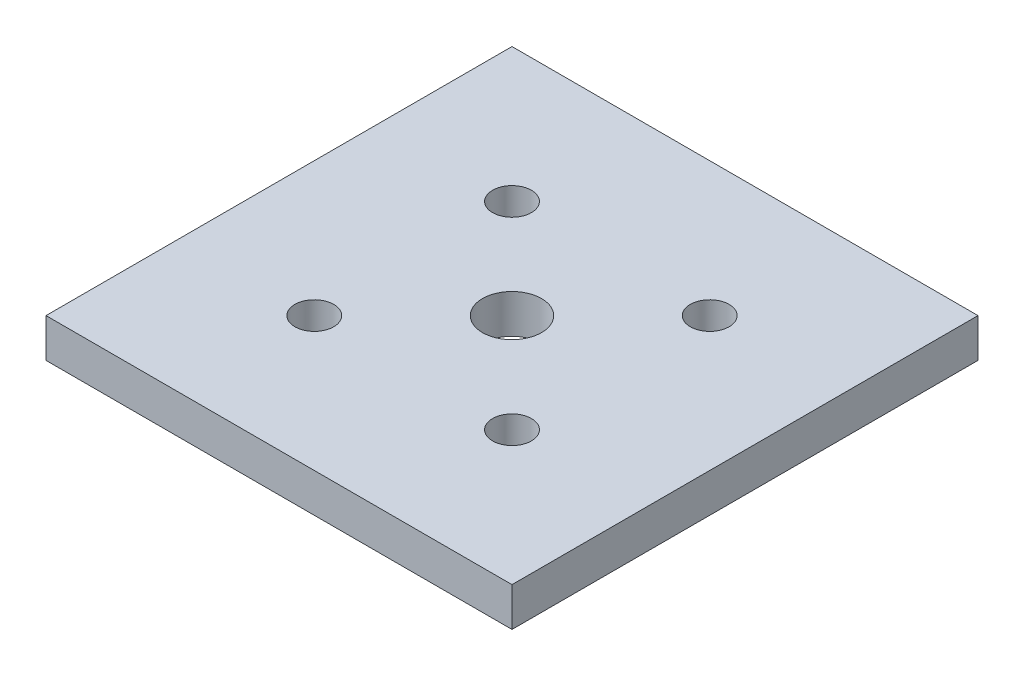
SolidWorks part; units mm, degrees
ref_plane "Front Plane" through (0, 0, 0) normal (0, 0, 1) x (1, 0, 0)
ref_plane "Top Plane" through (0, 0, 0) normal (0, 1, 0) x (1, 0, 0)
ref_plane "Right Plane" through (0, 0, 0) normal (1, 0, 0) x (0, 0, -1)
sketch "Sketch1" plane through (0, 0, 0) normal (0, 1, 0) x (1, 0, 0)
  line L0 (0, 28.2361) -> (0, -28.5398) construction
  line L1 (30, -30) -> (-30, -30)
  line L2 (30, -30) -> (30, 30)
  line L3 (30, 30) -> (-30, 30)
  line L4 (-30, -30) -> (-30, 30)
  line L5 (30, -30) -> (-30, 30) construction
  line L6 (30, 30) -> (-30, -30) construction
  line L7 (-35.2631, 0) -> (39.3471, 0) construction
  circle A0 centre (0, 0) radius 3.8
  circle A1 centre (-12.7279, 12.7279) radius 2.5
  circle A2 centre (12.7279, 12.7279) radius 2.5
  circle A3 centre (12.7279, -12.7279) radius 2.5
  circle A4 centre (-12.7279, -12.7279) radius 2.5
  point P0 (0, 0)
  dimension "D3" = 7.6
  dimension "D4" = 5
  dimension "D1" = 60
  dimension "D2" = 60
  dimension "D5" = 36
extrude "Boss-Extrude1" add sketch "Sketch1" along normal blind 5
